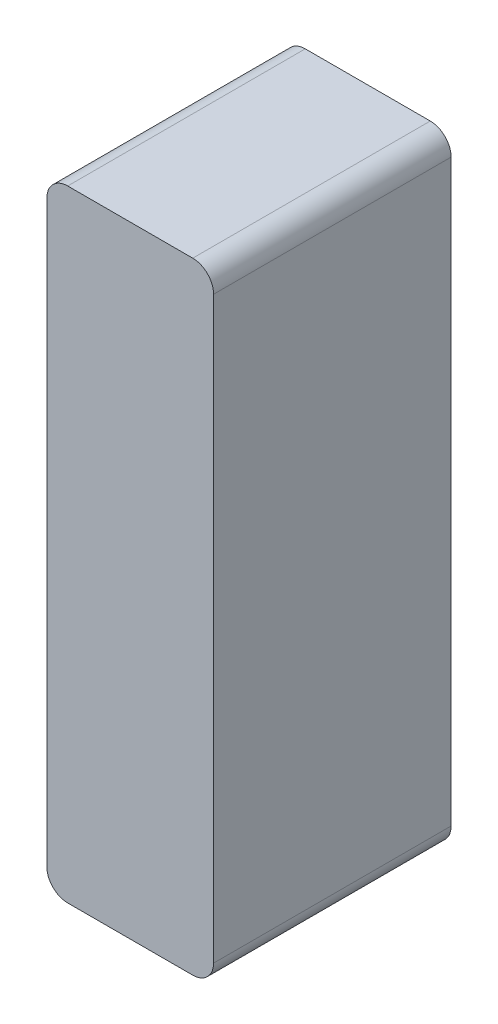
SolidWorks part; units mm, degrees
material "AISI 1020"
ref_plane "Alzado" through (0, 0, 0) normal (0, 0, 1) x (1, 0, 0)
ref_plane "Planta" through (0, 0, 0) normal (0, 1, 0) x (1, 0, 0)
ref_plane "Vista lateral" through (0, 0, 0) normal (1, 0, 0) x (0, 0, -1)
sketch "Croquis1" plane through (0, 0, 0) normal (0, 0, 1) x (1, 0, 0)
  line L1 (-4, -14.9) -> (4, -14.9)
  line L2 (-4, -14.9) -> (-4, 14.9)
  line L3 (-4, 14.9) -> (4, 14.9)
  line L4 (4, -14.9) -> (4, 14.9)
  line L5 (-4, -14.9) -> (4, 14.9) construction
  line L6 (-4, 14.9) -> (4, -14.9) construction
  point P0 (0, 0)
  dimension "D1" = 29.8
  dimension "D2" = 8
extrude "Saliente-Extruir1" add sketch "Croquis1" along normal blind 11.4
fillet "Redondeo2" radius 1 4 edges at (-4, -14.9, 5.7) (4, -14.9, 5.7) (-4, 14.9, 5.7) (4, 14.9, 5.7)
